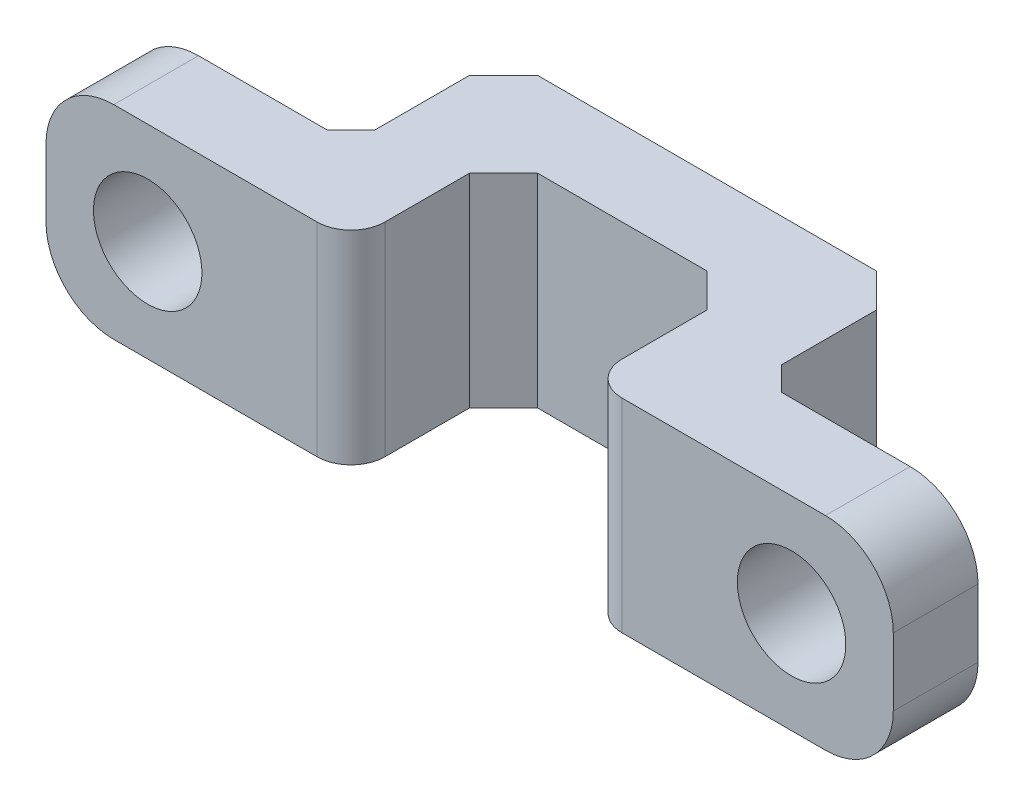
SolidWorks part; units mm, degrees
ref_plane "Front Plane" through (0, 0, 0) normal (0, 0, 1) x (1, 0, 0)
ref_plane "Top Plane" through (0, 0, 0) normal (0, 1, 0) x (1, 0, 0)
ref_plane "Right Plane" through (0, 0, 0) normal (1, 0, 0) x (0, 0, -1)
sketch "Sketch2" plane through (0, 0, 0) normal (0, 1, 0) x (1, 0, 0)
  line L1 (-3.5, -1.25) -> (3.5, -1.25)
  line L2 (-3.5, -1.25) -> (-3.5, 1.25)
  line L3 (-3.5, 1.25) -> (3.5, 1.25)
  line L4 (3.5, -1.25) -> (3.5, 1.25)
  line L5 (-3.5, -1.25) -> (3.5, 1.25) construction
  line L6 (-3.5, 1.25) -> (3.5, -1.25) construction
  line L7 (-3.5, 1.25) -> (-6, 1.25)
  line L8 (-3.5, 1.25) -> (-3.5, -5.75)
  line L9 (-3.5, -5.75) -> (-6, -5.75)
  line L10 (-6, 1.25) -> (-6, -5.75)
  line L11 (3.5, 1.25) -> (6, 1.25)
  line L12 (3.5, 1.25) -> (3.5, -5.75)
  line L13 (3.5, -5.75) -> (6, -5.75)
  line L14 (6, 1.25) -> (6, -5.75)
  line L15 (-6, -5.75) -> (-12.5, -5.75)
  line L16 (-6, -5.75) -> (-6, -3.25)
  line L17 (-6, -3.25) -> (-12.5, -3.25)
  line L18 (-12.5, -5.75) -> (-12.5, -3.25)
  line L19 (6, -5.75) -> (12.5, -5.75)
  line L20 (6, -5.75) -> (6, -3.25)
  line L21 (6, -3.25) -> (12.5, -3.25)
  line L22 (12.5, -5.75) -> (12.5, -3.25)
  point P0 (0, 0)
  dimension "D1" = 7
  dimension "D2" = 2.5
  dimension "D3" = 2.5
  dimension "D4" = 2.5
  dimension "D5" = 7
  dimension "D6" = 7
  dimension "D7" = 2.5
  dimension "D8" = 2.5
  dimension "D9" = 9
  dimension "D10" = 9
extrude "Boss-Extrude2" add sketch "Sketch2" along normal blind 6 contours L18 L15 L10 L17 | L7 L10 L9 L8 L2 | L1 L4 L3 L2 | L14 L11 L4 L12 L13 | L19 L22 L21 L14
sketch "Sketch3" plane through (0, 0, 3.25) normal (0, 0, -1) x (-1, 0, 0)
  line L2 (-6, 0) -> (-12.5, 0) construction
  line L3 (6, 0) -> (12.5, 0) construction
  circle A0 centre (-9.5, 3) radius 1.6
  circle A1 centre (9.5, 3) radius 1.6
  dimension "D1" = 3.2
  dimension "D3" = 3.2
  dimension "D2" = 9.5
  dimension "D4" = 9.5
  dimension "D5" = 3
  dimension "D6" = 3
extrude "Cut-Extrude1" cut sketch "Sketch3" against normal through all
chamfer "Chamfer1" distance 1 angle 45 4 edges at (-6, 3, -1.25) (6, 3, -1.25) (-3.5, 3, 1.25) (3.5, 3, 1.25)
fillet "Fillet1" radius 2 4 edges at (-12.5, 6, 4.5) (-12.5, 0, 4.5) (12.5, 6, 4.5) (12.5, 0, 4.5)
fillet "Fillet2" radius 1 2 edges at (-3.5, 3, 5.75) (3.5, 3, 5.75)
chamfer "Chamfer2" distance 0.7 angle 45 2 edges at (-6, 3, 3.25) (6, 3, 3.25)
